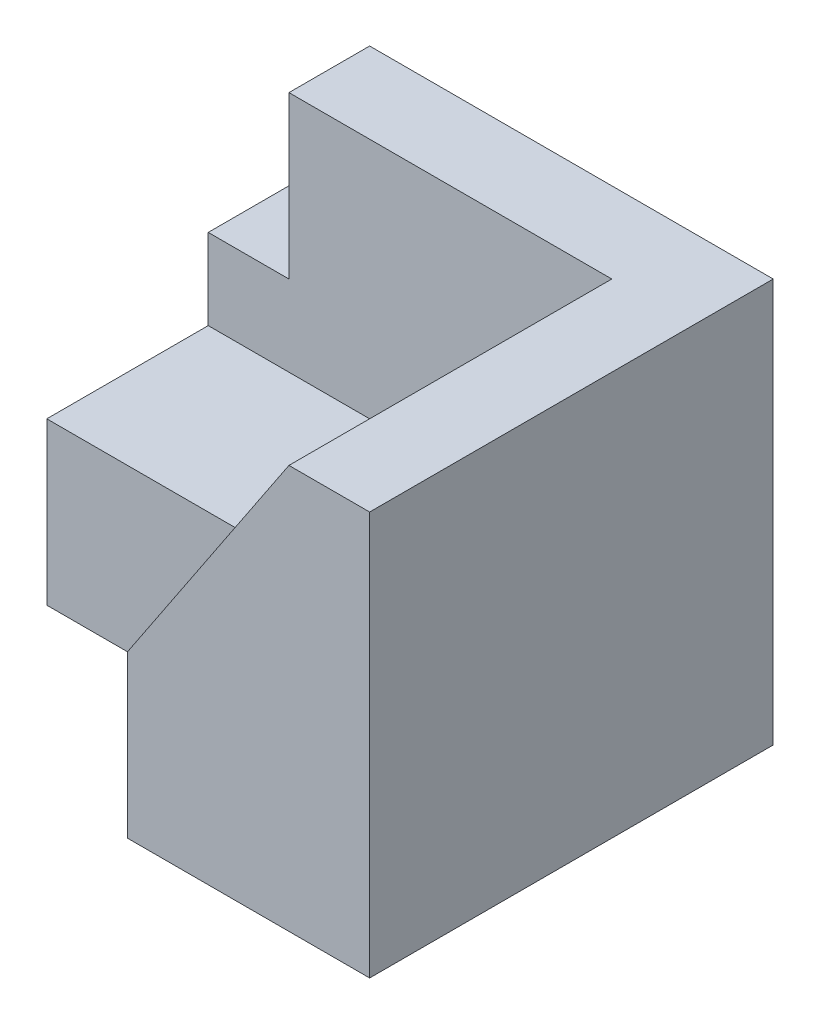
SolidWorks part; units mm, degrees
ref_plane "Front Plane" through (0, 0, 0) normal (0, 0, 1) x (1, 0, 0)
ref_plane "Top Plane" through (0, 0, 0) normal (0, 1, 0) x (1, 0, 0)
ref_plane "Right Plane" through (0, 0, 0) normal (1, 0, 0) x (0, 0, -1)
sketch "Sketch1" plane through (0, 0, 0) normal (0, 0, 1) x (1, 0, 0)
  line L1 (0, 0) -> (60, 0)
  line L2 (0, 0) -> (0, 50)
  line L3 (0, 50) -> (60, 50)
  line L4 (60, 0) -> (60, 50)
  dimension "D1" = 60
  dimension "D2" = 50
extrude "Boss-Extrude2" add sketch "Sketch1" along normal blind 50
sketch "Sketch2" plane through (0, 0, 50) normal (0, 0, 1) x (1, 0, 0)
  line L1 (0, 50) -> (10, 50)
  line L2 (0, 50) -> (0, 30)
  line L3 (0, 30) -> (10, 30)
  line L4 (10, 50) -> (10, 30)
  dimension "D1" = 10
  dimension "D2" = 20
extrude "Cut-Extrude1" cut sketch "Sketch2" against normal blind 50
sketch "Sketch3" plane through (0, 0, 50) normal (0, 0, 1) x (1, 0, 0)
  line L1 (0, 0) -> (30, 0)
  line L2 (0, 0) -> (0, 20)
  line L3 (0, 20) -> (30, 20)
  line L4 (30, 0) -> (30, 20)
  dimension "D1" = 30
  dimension "D2" = 20
extrude "Cut-Extrude2" cut sketch "Sketch3" against normal blind 20
sketch "Sketch4" plane through (0, 0, 50) normal (0, 0, 1) x (1, 0, 0)
  line L0 (30, 20) -> (50, 50)
  line L1 (60, 50) -> (10, 50) construction
  line L2 (50, 50) -> (10, 50)
  line L3 (10, 50) -> (10, 30)
  line L4 (10, 30) -> (0, 30)
  line L5 (0, 30) -> (0, 20)
  line L6 (0, 20) -> (30, 20)
  dimension "D1" = 20
extrude "Cut-Extrude4" cut sketch "Sketch4" against normal blind 40
